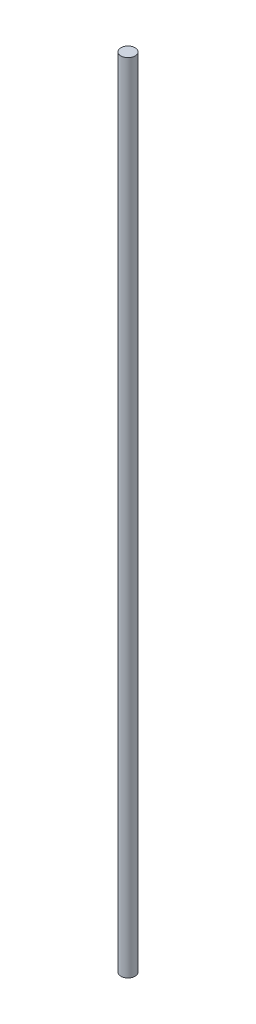
SolidWorks part; units mm, degrees
ref_plane "Front Plane" through (0, 0, 0) normal (0, 0, 1) x (1, 0, 0)
ref_plane "Top Plane" through (0, 0, 0) normal (0, 1, 0) x (1, 0, 0)
ref_plane "Right Plane" through (0, 0, 0) normal (1, 0, 0) x (0, 0, -1)
sketch "Sketch1" plane through (0, 0, 0) normal (0, 1, 0) x (1, 0, 0)
  circle A0 centre (0, 0) radius 4
extrude "Boss-Extrude1" add sketch "Sketch1" along normal blind 446
